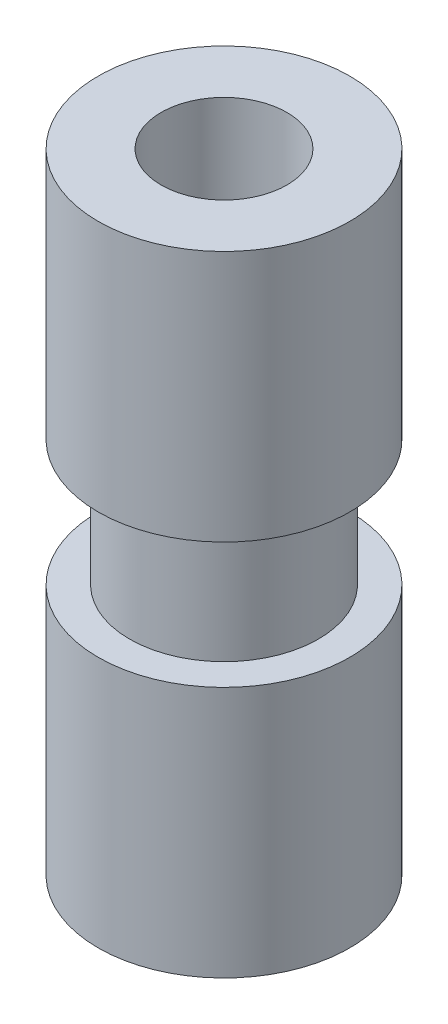
SolidWorks part; units mm, degrees
ref_plane "Front Plane" through (0, 0, 0) normal (0, 0, 1) x (1, 0, 0)
ref_plane "Top Plane" through (0, 0, 0) normal (0, 1, 0) x (1, 0, 0)
ref_plane "Right Plane" through (0, 0, 0) normal (1, 0, 0) x (0, 0, -1)
sketch "草图1" plane through (0, 0, 0) normal (0, 1, 0) x (1, 0, 0)
  circle A0 centre (0, 0) radius 2
  circle A1 centre (0, 0) radius 1
extrude "凸台-拉伸1" add sketch "草图1" along normal blind 6 and the other way blind 4
sketch "草图2" plane through (0, 0, 0) normal (0, 1, 0) x (1, 0, 0)
  circle A0 centre (0, 0) radius 2
  circle A1 centre (0, 0) radius 1.5
extrude "切除-拉伸1" cut sketch "草图2" along normal blind 2
sketch "草图3" plane through (0, -4, 0) normal (0, -1, 0) x (1, 0, 0)
  point P0 (0, 0)
sketch "草图4" plane through (0, 6, 0) normal (0, 1, 0) x (1, 0, 0)
  point P0 (0, 0)
